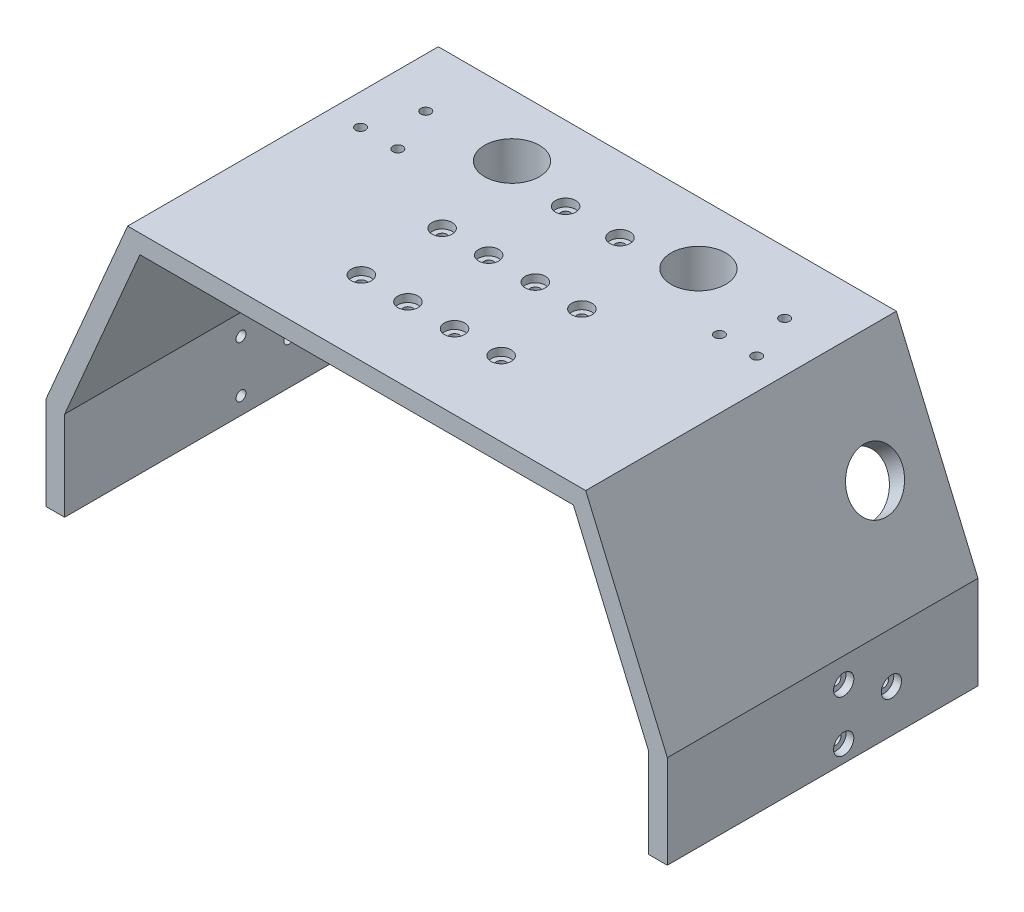
SolidWorks part; units mm, degrees
ref_plane "Alzado" through (0, 0, 0) normal (0, 0, 1) x (1, 0, 0)
ref_plane "Planta" through (0, 0, 0) normal (0, 1, 0) x (1, 0, 0)
ref_plane "Vista lateral" through (0, 0, 0) normal (1, 0, 0) x (0, 0, -1)
sketch "Croquis1" plane through (0, 0, 0) normal (0, 0, 1) x (1, 0, 0)
  line L1 (-100, 25) -> (-73.7179, 86.3249) construction
  line L2 (-73.7179, 86.3249) -> (73.7179, 86.3249) construction
  line L3 (100, 25) -> (100, -5) construction
  line L4 (100, 25) -> (73.7179, 86.3249) construction
  line L5 (-100, 25) -> (-100, -5)
  line L6 (-100, 25) -> (-73.7179, 86.3249)
  line L7 (-73.7179, 86.3249) -> (73.7179, 86.3249)
  line L8 (100, 25) -> (100, -5)
  line L9 (100, 25) -> (73.7179, 86.3249)
  line L10 (-94, 23.7685) -> (-94, -5)
  line L11 (-94, 23.7685) -> (-69.7615, 80.3249)
  line L12 (-69.7615, 80.3249) -> (69.7615, 80.3249)
  line L13 (94, 23.7685) -> (69.7615, 80.3249)
  line L14 (94, 23.7685) -> (94, -5)
  line L15 (-94, -5) -> (-100, -5)
  line L16 (100, -5) -> (94, -5)
  dimension "D2" = 30
  dimension "D1" = 6
extrude "Saliente-Extruir1" add sketch "Croquis1" along normal blind 100
sketch "Croquis3" plane through (0, 86.3249, 0) normal (0, 1, 0) x (1, 0, 0)
  line L0 (73.7179, 0) -> (-73.7179, 0) construction
  line L1 (73.7179, -100) -> (73.7179, 0) construction
  line L2 (-73.7179, -100) -> (-73.7179, 0) construction
  circle A2 centre (-30, -20) radius 8.8
  circle A3 centre (30, -20) radius 8.8
  dimension "D4" = 17.6
  dimension "D5" = 17.6
  dimension "D1" = 20
  dimension "D2" = 20
  dimension "D3" = 43.7179
  dimension "D6" = 43.7179
extrude "Cortar-Extruir1" cut sketch "Croquis3" against normal up to next
ref_plane "Plano1" through (-87.4795, 68.8361, 0) normal (-0.7859, 0.6184, 0) x (0, 0, -1)
sketch "Croquis4" plane through (-87.4795, 68.8361, 0) normal (-0.7859, 0.6184, 0) x (0, 0, -1)
  line L0 (0, -22.254) -> (0, 42.1921) construction
  line L1 (-100, -22.254) -> (0, -22.254) construction
  line L2 (-100, -22.254) -> (-100, 42.1921) construction
  line L3 (-100, 42.1921) -> (0, 42.1921) construction
  line L4 (0, -22.254) -> (0, 42.1921) construction
  line L5 (-100, -22.254) -> (0, -22.254) construction
  line L6 (-100, -22.254) -> (-100, 42.1921) construction
  line L7 (-100, 42.1921) -> (0, 42.1921) construction
  line L8 (0, 9.9691) -> (-100, 9.9691) construction
  circle A0 centre (-20, 9.9691) radius 8.8
  dimension "D1" = 17.6
  dimension "D2" = 20
extrude "Cortar-Extruir2" cut sketch "Croquis4" against normal up to next
mirror "Simetría1" about plane through (0, 0, 0) normal (1, 0, 0) of "Cortar-Extruir2"
sketch "Croquis5" plane through (0, 80.3249, 0) normal (0, -1, 0) x (1, 0, 0)
  line L0 (15.175, 0) -> (15.175, 2.3)
  line L1 (15.175, 2.3) -> (3.7842, 2.3)
  line L3 (-3.7842, 2.3) -> (-15.175, 2.3)
  line L4 (-15.175, 2.3) -> (-15.175, 0)
  line L10 (-14.875, 0) -> (-3.2619, 0)
  line L11 (3.2619, 0) -> (14.875, 0)
  line L12 (14.875, 0) -> (14.875, 2)
  line L13 (14.875, 2) -> (3.7202, 2)
  line L14 (-3.7202, 2) -> (-14.875, 2)
  line L15 (-14.875, 2) -> (-14.875, 0)
  line L17 (-15.175, 0) -> (3.2619, 0)
  line L19 (-3.2619, 0) -> (15.175, 0)
  line L20 (14.875, 0) -> (14.875, 2)
  line L22 (14.875, 2) -> (3.7202, 2)
  line L23 (-3.7202, 2) -> (-14.875, 2)
  line L24 (-14.875, 2) -> (-14.875, 0)
  arc A0 (3.7842, 2.3) -> (-3.7842, 2.3) centre (0, -6.25) ccw
  arc A3 (3.2619, 0) -> (-3.2619, 0) centre (0, -6.25) ccw
  arc A4 (3.7202, 2) -> (-3.7202, 2) centre (0, -6.25) ccw
  arc A5 (3.2619, 0) -> (-3.2619, 0) centre (0, -6.25) ccw
  arc A7 (3.7202, 2) -> (-3.7202, 2) centre (0, -6.25) ccw
  dimension "D1" = 0
  dimension "D2" = 0.3
extrude "Cortar-Extruir3" cut sketch "Croquis5" against normal blind 0.5
sketch "Croquis6" plane through (-100, 0, 0) normal (-1, 0, 0) x (0, 0, 1)
  circle A0 centre (43.227, 0.4977) radius 1.6 construction
  circle A1 centre (27.8635, 8.7685) radius 1.6 construction
  circle A2 centre (43.227, 17.0392) radius 1.6 construction
  circle A3 centre (43.227, 0.4977) radius 1.6
  circle A4 centre (27.8635, 8.7685) radius 1.6
  circle A5 centre (43.227, 17.0392) radius 1.6
extrude "Cortar-Extruir4" cut sketch "Croquis6" against normal up to next
sketch "Croquis7" plane through (-100, 0, 0) normal (-1, 0, 0) x (0, 0, 1)
  circle A0 centre (27.8635, 8.7685) radius 3.25
  circle A1 centre (43.227, 0.4977) radius 3.25
  circle A2 centre (43.227, 17.0392) radius 3.25
  dimension "D1" = 6.5
extrude "Cortar-Extruir5" cut sketch "Croquis7" against normal blind 2.5
mirror "Simetría2" about plane through (0, 0, 0) normal (1, 0, 0) of "Cortar-Extruir5", "Cortar-Extruir4"
sketch "Croquis8" plane through (0, 80.3249, 0) normal (0, -1, 0) x (1, 0, 0)
  line L0 (0, 100) -> (0, 0) construction
  line L1 (-37.5, 82) -> (37.5, 82)
  line L3 (-37.5, 70) -> (37.5, 70)
  line L5 (-69.7615, 100) -> (69.7615, 100) construction
  line L7 (-37.5, 56) -> (37.5, 56)
  line L8 (-37.5, 56) -> (-37.5, 44)
  line L9 (-37.5, 44) -> (37.5, 44)
  line L10 (37.5, 56) -> (37.5, 44)
  line L11 (-69.7615, 50) -> (69.7615, 50) construction
  line L12 (-69.7615, 100) -> (-69.7615, 0) construction
  line L13 (69.7615, 100) -> (69.7615, 0) construction
  line L14 (-17.5, 30) -> (17.5, 30)
  line L15 (-17.5, 30) -> (-17.5, 18)
  line L16 (-17.5, 18) -> (17.5, 18)
  line L17 (17.5, 30) -> (17.5, 18)
  line L19 (-73.7179, 0) -> (73.7179, 0) construction
  line L20 (-37.5, 76) -> (37.5, 76) construction
  line L21 (-37.5, 70) -> (-37.5, 82)
  line L24 (37.5, 82) -> (37.5, 70)
  point P29 (37.5, 76)
  dimension "D1" = 12
  dimension "D3" = 12
  dimension "D4" = 30
  dimension "D5" = 75
  dimension "D6" = 12
  dimension "D7" = 30
  dimension "D8" = 35
  dimension "D9" = 75
extrude "Cortar-Extruir6" cut sketch "Croquis8" against normal blind 2.5
sketch "Croquis9" plane through (0, 82.8249, 0) normal (0, -1, 0) x (1, 0, 0)
  line L0 (-37.4, 76) -> (37.4, 76) construction
  line L1 (-37.5, 50) -> (37.5, 50) construction
  line L2 (-37.5, 56) -> (-37.5, 44) construction
  line L3 (-37.4, 81.9) -> (-37.4, 70.1) construction
  line L4 (37.5, 44) -> (37.5, 56) construction
  line L5 (-17.5, 24) -> (17.5, 24) construction
  line L6 (37.4, 70.1) -> (37.4, 81.9) construction
  line L7 (-37.5, 82) -> (-37.5, 70) construction
  line L8 (73.7179, 0) -> (-73.7179, 0)
  line L9 (73.7179, -6) -> (73.7179, 0)
  line L10 (-73.7179, -6) -> (73.7179, -6)
  line L11 (-73.7179, 0) -> (-73.7179, -6)
  line L12 (73.7179, 0) -> (-73.7179, 0) construction
  line L14 (0, 100) -> (0, 0) construction
  line L15 (-69.7615, 100) -> (69.7615, 100) construction
  line L23 (-17.5, 30) -> (-17.5, 18) construction
  line L24 (17.5, 18) -> (17.5, 30) construction
  line L25 (-37.5, 56) -> (-37.5, 44) construction
  line L28 (0, 18) -> (-17.5, 30) construction
  line L29 (-17.5, 18) -> (17.5, 18) construction
  line L30 (0, 30) -> (-17.5, 18) construction
  line L31 (17.5, 30) -> (-17.5, 30) construction
  circle A7 centre (-22.5, 76) radius 1.6
  circle A8 centre (-7.5, 76) radius 1.6
  circle A9 centre (7.5, 76) radius 1.6
  circle A10 centre (22.5, 76) radius 1.6
  circle A15 centre (-22.5, 50) radius 1.6
  circle A16 centre (-7.5, 50) radius 1.6
  circle A17 centre (7.5, 50) radius 1.6
  circle A18 centre (22.5, 50) radius 1.6
  circle A19 centre (-8.75, 24) radius 1.6
  circle A21 centre (8.75, 24) radius 1.6
  dimension "D1" = 3.2
  dimension "D2" = 15
  dimension "D3" = 15
  dimension "D4" = 15
  dimension "D7" = 15
  dimension "D11" = 3.2
  dimension "D13" = 3.2
  dimension "D5" = 15
  dimension "D6" = 0
  dimension "D8" = 15
  dimension "D10" = 15
  dimension "D9" = 15
extrude "Cortar-Extruir7" cut sketch "Croquis9" against normal up to next
sketch "Croquis10" plane through (0, 86.3249, 0) normal (0, 1, 0) x (1, 0, 0)
  circle A0 centre (-22.5, -50) radius 3.25
  circle A1 centre (-7.5, -50) radius 3.25
  circle A2 centre (7.5, -50) radius 3.25
  circle A3 centre (22.5, -50) radius 3.25
  circle A4 centre (8.75, -24) radius 3.25
  circle A5 centre (-8.75, -24) radius 3.25
  circle A6 centre (22.5, -50) radius 1.6 construction
  circle A7 centre (7.5, -50) radius 1.6 construction
  circle A8 centre (-7.5, -50) radius 1.6 construction
  circle A9 centre (-22.5, -50) radius 1.6 construction
  circle A10 centre (22.5, -76) radius 3.25
  circle A11 centre (7.5, -76) radius 3.25
  circle A12 centre (-7.5, -76) radius 3.25
  circle A13 centre (-22.5, -76) radius 3.25
  circle A14 centre (-8.75, -24) radius 1.6 construction
  circle A15 centre (8.75, -24) radius 1.6 construction
  dimension "D1" = 6.5
  dimension "D2" = 6.5
  dimension "D3" = 6.5
  dimension "D4" = 6.5
  dimension "D5" = 6.5
extrude "Cortar-Extruir8" cut sketch "Croquis10" against normal blind 2.5
sketch "Croquis11" plane through (0, 80.3249, 0) normal (0, -1, 0) x (1, 0, 0)
  circle A0 centre (30, 20) radius 8.8 construction
  circle A1 centre (-30, 20) radius 8.8 construction
  circle A2 centre (30, 20) radius 8.8
  circle A3 centre (-30, 20) radius 8.8
  circle A4 centre (-30, 20) radius 10.3
  circle A5 centre (30, 20) radius 10.3
  dimension "D1" = 1.5
extrude "Saliente-Extruir2" add sketch "Croquis11" along normal blind 10
ref_plane "Plano2" through (-63.9034, 50.2844, 0) normal (-0.7859, 0.6184, 0) x (0, 0, -1)
sketch "Croquis12" plane through (-63.9034, 50.2844, 0) normal (-0.7859, 0.6184, 0) x (0, 0, -1)
  circle A0 centre (-20, 9.9691) radius 8.8 construction
  circle A1 centre (-20, 9.9691) radius 8.8
  circle A2 centre (-20, 9.9691) radius 10.3
  dimension "D1" = 1.5
extrude "Saliente-Extruir3" add sketch "Croquis12" along normal up to next
sketch "Croquis13" plane through (0, 80.3249, 0) normal (0, -1, 0) x (1, 0, 0)
  circle A0 centre (57.7615, 20) radius 1.6 construction
  circle A1 centre (51.7615, 35) radius 1.6 construction
  circle A2 centre (63.7615, 35) radius 1.6 construction
  circle A3 centre (-57.7615, 20) radius 1.6 construction
  circle A4 centre (-63.7615, 35) radius 1.6 construction
  circle A5 centre (-51.7615, 35) radius 1.6 construction
  circle A6 centre (57.7615, 20) radius 1.6
  circle A7 centre (51.7615, 35) radius 1.6
  circle A8 centre (63.7615, 35) radius 1.6
  circle A9 centre (-57.7615, 20) radius 1.6
  circle A10 centre (-63.7615, 35) radius 1.6
  circle A11 centre (-51.7615, 35) radius 1.6
extrude "Cortar-Extruir9" cut sketch "Croquis13" against normal up to next
